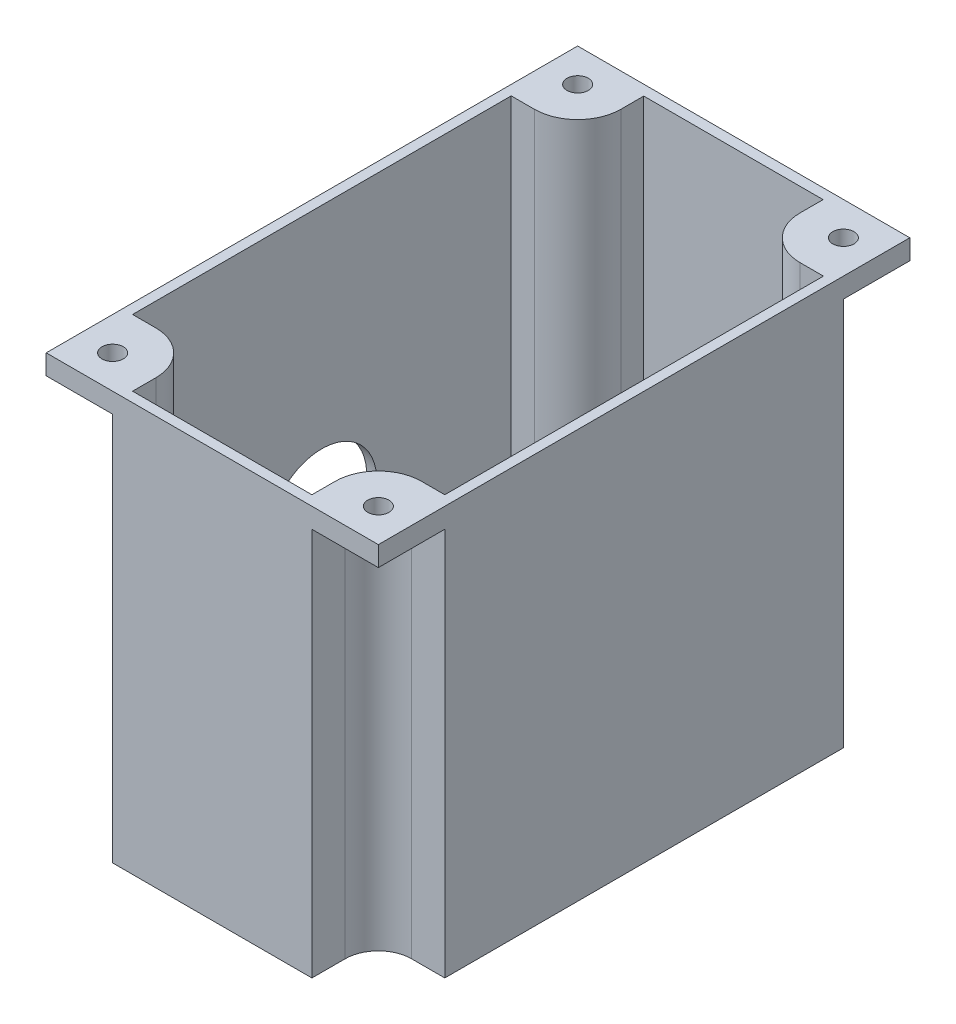
SolidWorks part; units mm, degrees
ref_plane "Płaszczyzna przednia" through (0, 0, 0) normal (0, 0, 1) x (1, 0, 0)
ref_plane "Płaszczyzna górna" through (0, 0, 0) normal (0, 1, 0) x (1, 0, 0)
ref_plane "Płaszczyzna prawa" through (0, 0, 0) normal (1, 0, 0) x (0, 0, -1)
sketch "Sketch1" plane through (0, 0, 0) normal (0, 1, 0) x (1, 0, 0)
  line L4 (23.5, 28.5) -> (23.5, -28.5)
  line L9 (-25, -40) -> (25, -40)
  line L16 (-25, -40) -> (-25, 40)
  line L21 (-25, 40) -> (25, 40)
  line L23 (25, -40) -> (25, 40)
  line L27 (-25, -30) -> (-25, 30)
  line L29 (25, -30) -> (25, 30)
  line L30 (25, 40) -> (15, 40)
  line L31 (25, 40) -> (25, 30)
  line L32 (25, 30) -> (20, 30)
  line L33 (15, 40) -> (15, 35)
  line L34 (25, -40) -> (15, -40)
  line L35 (25, -40) -> (25, -30)
  line L36 (25, -30) -> (20, -30)
  line L37 (15, -40) -> (15, -35)
  line L38 (-25, -40) -> (-15, -40)
  line L39 (-25, -40) -> (-25, -30)
  line L40 (-25, -30) -> (-20, -30)
  line L41 (-15, -40) -> (-15, -35)
  line L42 (-25, 40) -> (-15, 40)
  line L43 (-25, 40) -> (-25, 30)
  line L44 (-25, 30) -> (-20, 30)
  line L45 (-15, 40) -> (-15, 35)
  line L46 (25, 40) -> (13.5, 40)
  line L47 (25, 40) -> (25, 28.5)
  line L48 (23.5, 28.5) -> (20, 28.5)
  line L49 (13.5, 38.45) -> (13.5, 35)
  line L50 (25, -40) -> (13.5, -40)
  line L51 (25, -40) -> (25, -28.5)
  line L52 (23.5, -28.5) -> (20, -28.5)
  line L53 (13.5, -38.5) -> (13.5, -35)
  line L54 (-25, 40) -> (-13.5, 40)
  line L55 (-25, 40) -> (-25, 28.5)
  line L56 (-23.5, 28.5) -> (-20, 28.5)
  line L57 (-13.5, 38.45) -> (-13.5, 35)
  line L58 (-25, -40) -> (-13.5, -40)
  line L59 (-25, -40) -> (-25, -28.5)
  line L60 (-23.5, -28.5) -> (-20, -28.5)
  line L61 (-13.5, -38.5) -> (-13.5, -35)
  line L62 (13.5, -38.5) -> (-13.5, -38.5)
  line L63 (-23.5, -28.5) -> (-23.5, 28.5)
  line L64 (-13.5, 38.45) -> (13.5, 38.45)
  arc A0 (-20, 30) -> (-15, 35) centre (-20, 35) ccw
  arc A1 (-20, -30) -> (-15, -35) centre (-20, -35) cw
  arc A2 (20, -30) -> (15, -35) centre (20, -35) ccw
  arc A3 (20, 30) -> (15, 35) centre (20, 35) cw
  arc A4 (20, 28.5) -> (13.5, 35) centre (20, 35) cw
  arc A5 (20, -28.5) -> (13.5, -35) centre (20, -35) ccw
  arc A6 (-20, -28.5) -> (-13.5, -35) centre (-20, -35) cw
  arc A7 (-20, 28.5) -> (-13.5, 35) centre (-20, 35) ccw
  point P0 (0, 0)
  point P1 (0, 0)
  point P5 (0, 0)
  point P8 (0, 0)
  point P11 (0, 0)
  point P14 (0, 0)
  point P27 (-15, -30)
  point P32 (15, 30)
  point P47 (13.5, 28.5)
  point P50 (13.5, -28.5)
  point P55 (-13.5, 28.5)
  point P56 (23.5, 28.5)
  point P59 (13.5, -38.5)
  point P62 (-23.5, -28.5)
  point P65 (-13.5, 38.45)
  dimension "D6" = 5
  dimension "D11" = 6.5
  dimension "D1" = 50
  dimension "D2" = 80
  dimension "D3" = 50
  dimension "D4" = 10
  dimension "D5" = 10
  dimension "D7" = 11.5
  dimension "D8" = 11.5
  dimension "D9" = 11.5
  dimension "D10" = 11.5
  dimension "D12" = 1.5
  dimension "D13" = 1.5
  dimension "D14" = 1.5
  dimension "D15" = 1.55
extrude "Boss-Extrude6" add sketch "Sketch1" along normal blind 60
sketch "Sketch7" plane through (0, 0, 0) normal (0, -1, 0) x (1, 0, 0)
  line L0 (-15, 40) -> (15, 40)
  line L5 (15, 40) -> (15, 35)
  line L6 (20, 30) -> (25, 30)
  line L7 (25, 30) -> (25, -30)
  line L8 (25, -30) -> (20, -30)
  line L9 (15, -35) -> (15, -40)
  line L10 (15, -40) -> (-15, -40)
  line L11 (-15, -40) -> (-15, -35)
  line L12 (-20, -30) -> (-25, -30)
  line L13 (-25, -30) -> (-25, 30)
  line L14 (-25, 30) -> (-20, 30)
  line L15 (-15, 35) -> (-15, 40)
  arc A0 (-20, 30) -> (-15, 35) centre (-20, 35) ccw
  arc A1 (-15, -35) -> (-20, -30) centre (-20, -35) ccw
  arc A2 (20, -30) -> (15, -35) centre (20, -35) ccw
  arc A3 (15, 35) -> (20, 30) centre (20, 35) ccw
  dimension "D1" = 5
extrude "Boss-Extrude8" add sketch "Sketch7" along normal blind 1.5
sketch "Sketch12" plane through (0, 60, 0) normal (0, 1, 0) x (1, 0, 0)
  line L0 (-25, 40) -> (-15, 40)
  line L1 (-25, 30) -> (-15, 30) construction
  line L2 (-25, 30) -> (-25, 40) construction
  line L3 (-25, 40) -> (-15, 40) construction
  line L4 (-15, 30) -> (-15, 40) construction
  line L5 (15, 40) -> (25, 40) construction
  line L6 (15, 40) -> (15, 30) construction
  line L7 (15, 30) -> (25, 30) construction
  line L8 (25, 40) -> (25, 30) construction
  line L9 (-25, -30) -> (-15, -30) construction
  line L10 (-25, -30) -> (-25, -40) construction
  line L11 (-25, -40) -> (-15, -40) construction
  line L12 (-15, -30) -> (-15, -40) construction
  line L13 (15, -40) -> (25, -40) construction
  line L14 (15, -40) -> (15, -30) construction
  line L15 (15, -30) -> (25, -30) construction
  line L16 (25, -40) -> (25, -30) construction
  line L17 (-15, 40) -> (-15, 35)
  line L18 (-20, 30) -> (-25, 30)
  line L19 (-25, 30) -> (-25, 40)
  line L20 (15, 40) -> (25, 40)
  line L21 (25, 40) -> (25, 30)
  line L22 (25, 30) -> (20, 30)
  line L23 (15, 35) -> (15, 40)
  line L24 (20, -30) -> (25, -30)
  line L25 (25, -30) -> (25, -40)
  line L26 (25, -40) -> (15, -40)
  line L27 (15, -40) -> (15, -35)
  line L28 (-15, -40) -> (-25, -40)
  line L29 (-25, -40) -> (-25, -30)
  line L30 (-25, -30) -> (-20, -30)
  line L31 (-15, -35) -> (-15, -40)
  arc A0 (-15, 35) -> (-20, 30) centre (-20, 35) cw
  arc A1 (20, 30) -> (15, 35) centre (20, 35) cw
  arc A2 (20, -30) -> (15, -35) centre (20, -35) ccw
  arc A3 (-20, -30) -> (-15, -35) centre (-20, -35) cw
  dimension "D1" = 5
extrude "Boss-Extrude9" add sketch "Sketch12" against normal blind 3
sketch "Sketch15" plane through (0, 60, 0) normal (0, 1, 0) x (1, 0, 0)
  circle A0 centre (-20, -35) radius 1.6
  circle A1 centre (20, -35) radius 1.6
  circle A2 centre (20, 35) radius 1.6
  circle A3 centre (-20, 35) radius 1.6
extrude "Cut-Extrude4" cut sketch "Sketch15" against normal through all
sketch "Sketch11" plane through (-25, 0, 0) normal (-1, 0, 0) x (0, 0, 1)
  line L0 (0, 60) -> (0, -1.5) construction
  line L1 (40, 60) -> (-40, 60) construction
  line L2 (30, -1.5) -> (-30, -1.5) construction
  line L3 (-21.9493, 60) -> (-21.9493, 20) construction
  line L4 (-21.9493, 20) -> (0, 20) construction
  circle A1 centre (0, 20) radius 8.25
  point P9 (0.6695, 20)
  dimension "D1" = 40
extrude "Cut-Extrude3" cut sketch "Sketch11" against normal blind 1.5
